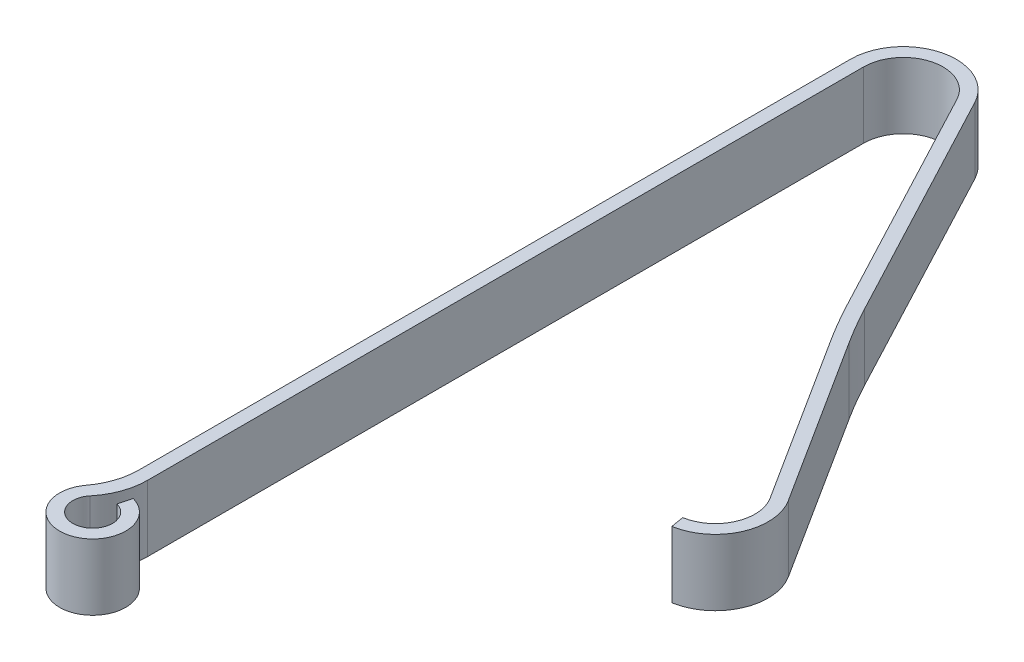
SolidWorks part; units mm, degrees
material "Stainless Steel (ferritic)"
ref_plane "Front Plane" through (0, 0, 0) normal (0, 0, 1) x (1, 0, 0)
ref_plane "Top Plane" through (0, 0, 0) normal (0, 1, 0) x (1, 0, 0)
ref_plane "Right Plane" through (0, 0, 0) normal (1, 0, 0) x (0, 0, -1)
sketch "Sketch1" plane through (0, 0, 0) normal (0, 1, 0) x (1, 0, 0)
  line L0 (0, 0) -> (0, 14.224)
  line L1 (1.9142, 14.6989) -> (4.2885, 10.2079)
  line L2 (4.699, 9.5018) -> (6.7445, 6.2875)
  line L3 (0.254, -0.201) -> (0.254, 14.224)
  line L4 (1.6896, 14.5802) -> (4.064, 10.0892)
  line L5 (4.4847, 9.3654) -> (6.5303, 6.1511)
  line L7 (6.0131, 4.9904) -> (6.055, 4.7399)
  line L8 (0.4184, 0.0314) -> (0.3526, -0.214)
  line L9 (0, 0) -> (0, 14.224) construction
  line L10 (0.254, 0) -> (0.254, 14.224) construction
  line L13 (0, 0) -> (0, -1.7215) construction
  arc A0 (0, 14.224) -> (1.9142, 14.6989) centre (1.016, 14.224) cw
  arc A1 (4.2885, 10.2079) -> (4.699, 9.5018) centre (13.2705, 14.9566) ccw
  arc A2 (6.7445, 6.2875) -> (6.055, 4.7399) centre (5.8874, 5.742) cw
  arc A3 (0.254, 14.224) -> (1.6896, 14.5802) centre (1.016, 14.224) cw
  arc A4 (4.064, 10.0892) -> (4.4847, 9.3654) centre (13.2705, 14.9566) ccw
  arc A5 (6.5303, 6.1511) -> (6.0131, 4.9904) centre (5.8874, 5.742) cw
  arc A6 (6.7445, 6.2875) -> (6.055, 4.7399) centre (5.8874, 5.742) cw construction
  arc A7 (0, 0) -> (0.4184, 0.0314) centre (0.254, -0.582) ccw
  arc A8 (0.254, -0.201) -> (0.3526, -0.214) centre (0.254, -0.582) ccw
  circle A9 centre (0.254, -0.582) radius 0.635 construction
  circle A10 centre (0.254, -0.582) radius 0.381 construction
  point P21 (4.2671, 9.7231)
  point P22 (6.8154, 5.3285)
  dimension "D4" = 1.016
  dimension "D5" = 1.016
  dimension "D6" = 5.08
  dimension "D8" = 10.16
  dimension "D2" = 15.24
  dimension "D11" = 1.27
  dimension "D3" = 5.08
  dimension "D7" = 3.81
  dimension "D9" = 3.81
  dimension "D10" = 0.254
  dimension "D12" = 15
  dimension "D13" = 7.62
  dimension "D1" = 0.254
extrude "Boss-Extrude1" add sketch "Sketch1" along normal blind 1.27
fillet "Fillet1" radius 1.27 2 edges at (0, 0.635, 0) (0.254, 0.635, 0.201)
